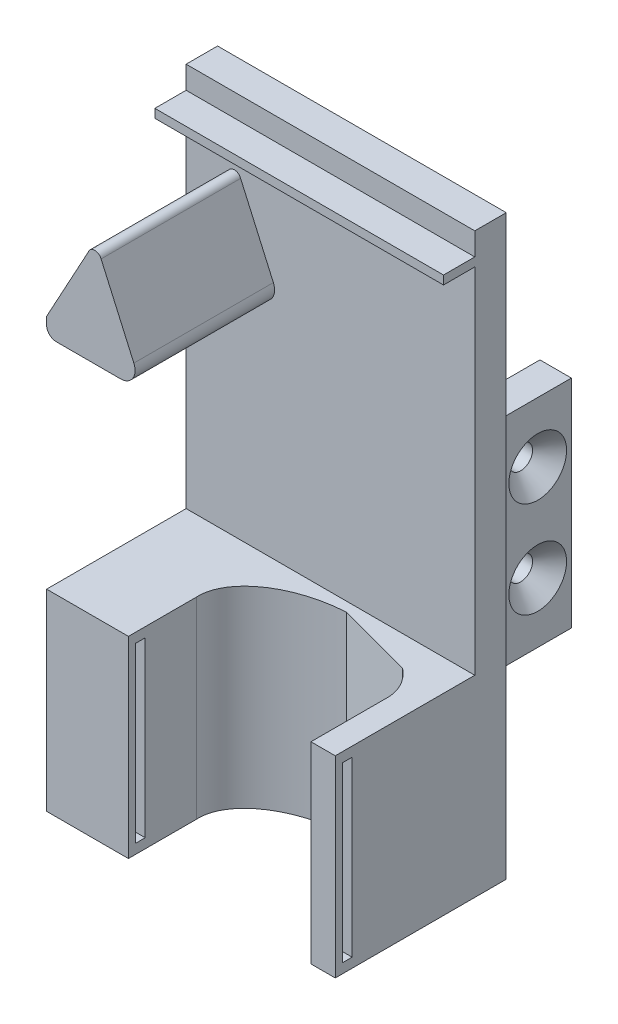
SolidWorks part; units mm, degrees
ref_plane "Front Plane" through (0, 0, 0) normal (0, 0, 1) x (1, 0, 0)
ref_plane "Top Plane" through (0, 0, 0) normal (0, 1, 0) x (1, 0, 0)
ref_plane "Right Plane" through (0, 0, 0) normal (1, 0, 0) x (0, 0, -1)
sketch "Sketch1" plane through (0, 0, 0) normal (0, 0, 1) x (1, 0, 0)
  line L1 (-30, 60) -> (30, 60)
  line L2 (-30, 60) -> (-30, -60)
  line L3 (-30, -60) -> (30, -60)
  line L4 (30, 60) -> (30, -60)
  line L5 (-30, 60) -> (30, -60) construction
  line L6 (-30, -60) -> (30, 60) construction
  point P0 (0, 0)
  dimension "D1" = 60
  dimension "D2" = 120
extrude "Boss-Extrude1" add sketch "Sketch1" along normal blind 6.54
sketch "Sketch7" plane through (0, 0, 6.54) normal (0, 0, 1) x (1, 0, 0)
  line L0 (-10, 25.5339) -> (-18.6733, 45.1016)
  line L1 (-30, 25.5339) -> (-10, 25.5339)
  line L6 (30, -60) -> (30, 60) construction
  line L15 (-21.3057, 45.0714) -> (-30, 29.1154)
  line L16 (-30, 60) -> (-30, -60) construction
  line L18 (-30, 29.1154) -> (-30, 25.5339)
  line L19 (30, 60) -> (-30, 60) construction
  arc A1 (-21.3057, 45.0714) -> (-18.6733, 45.1016) centre (-19.9839, 44.595) cw
  point P3 (-20, 46)
  dimension "D1" = 14
  dimension "D3" = 20
  dimension "D4" = 40
  dimension "D2" = 50
sketch "Sketch10" plane through (0, 0, 0) normal (0, 0, -1) x (-1, 0, 0)
  line L1 (20, 20) -> (26.54, 20)
  line L2 (-20, -25) -> (-20, 20)
  line L4 (-20, 20) -> (-26.54, 20)
  line L7 (20, -25) -> (20, 20)
  line L10 (-26.54, 20) -> (-26.54, -25)
  line L11 (-26.54, -25) -> (-20, -25)
  line L12 (26.54, 20) -> (26.54, -25)
  line L13 (26.54, -25) -> (20, -25)
  dimension "D1" = 6.54
  dimension "D2" = 20
  dimension "D3" = 6.54
  dimension "D4" = 20
  dimension "D5" = 45
  dimension "D6" = 45
extrude "Boss-Extrude5" add sketch "Sketch10" along normal blind 17
sketch "Sketch17" plane through (0, 0, 6.54) normal (0, 0, 1) x (1, 0, 0)
  line L0 (-30, 60) -> (-30, -60) construction
  line L1 (-30, -20) -> (30, -20)
  line L2 (-30, -20) -> (-30, -60)
  line L3 (-30, -60) -> (30, -60)
  line L4 (30, -20) -> (30, -60)
  line L5 (30, -60) -> (30, 60) construction
  line L6 (-30, -60) -> (30, -60) construction
  line L7 (30, 60) -> (-30, 60) construction
  dimension "D1" = 40
  dimension "D2" = 0
  dimension "D3" = 80
extrude "Boss-Extrude6" add sketch "Sketch17" along normal blind 29
sketch "Sketch18" plane through (0, -20, 0) normal (0, 1, 0) x (1, 0, 0)
  line L0 (5.335, -8.5264) -> (21.2913, -12.8258)
  line L1 (30, -35.54) -> (30, -6.54) construction
  line L2 (30, -35.54) -> (-30, -35.54) construction
  ellipse E0 centre (5.9723, -20.3092) end of major axis (24.9445, -19.283) minor radius 11.8 (5.335, -8.5264) -> (21.2913, -12.8258) ccw
  dimension "D1" = 43
  dimension "D2" = 5.0555
  dimension "D3" = 3.448
extrude "Cut-Extrude1" cut sketch "Sketch18" against normal up to next contours E0 L0
sketch "Sketch21" plane through (0, 0, 35.54) normal (0, 0, 1) x (1, 0, 0)
  line L0 (30, -20) -> (-30, -20) construction
  line L1 (-13, -20) -> (24.9445, -20)
  line L2 (-13, -20) -> (-13, -60)
  line L3 (-13, -60) -> (24.9445, -60)
  line L4 (24.9445, -20) -> (24.9445, -60)
  line L5 (-30, -60) -> (30, -60) construction
  line L6 (30, -60) -> (30, -20) construction
  dimension "D1" = 5.0555
  dimension "D2" = 43
extrude "Cut-Extrude2" cut sketch "Sketch21" against normal up to next contours L2 L3 L4 L1
sketch "Sketch23" plane through (-13, 0, 0) normal (1, 0, 0) x (0, 0, -1)
  line L0 (-35.54, -20) -> (-35.54, -60) construction
  line L1 (-34.04, -22) -> (-32.04, -22)
  line L2 (-34.04, -22) -> (-34.04, -58)
  line L3 (-34.04, -58) -> (-32.04, -58)
  line L4 (-32.04, -22) -> (-32.04, -58)
  line L5 (-21.3353, -60) -> (-35.54, -60) construction
  line L6 (-21.3353, -20) -> (-35.54, -20) construction
  dimension "D1" = 3.5
  dimension "D2" = 2
  dimension "D3" = 2
  dimension "D4" = 2
  dimension "D5" = 36
extrude "Cut-Extrude3" cut sketch "Sketch23" against normal blind 9
sketch "Sketch24" plane through (24.9445, 0, 0) normal (-1, 0, 0) x (0, 0, 1)
  line L0 (20.076, -60) -> (35.54, -60) construction
  line L1 (32.04, -22) -> (34.04, -22)
  line L2 (32.04, -22) -> (32.04, -58)
  line L3 (32.04, -58) -> (34.04, -58)
  line L4 (34.04, -22) -> (34.04, -58)
  line L5 (20.076, -20) -> (35.54, -20) construction
  line L6 (35.54, -20) -> (35.54, -60) construction
  dimension "D1" = 2
  dimension "D2" = 2
  dimension "D3" = 2
  dimension "D4" = 3.5
extrude "Cut-Extrude4" cut sketch "Sketch24" against normal blind 9
hole_wizard "CSK for M3 Flat Head Machine Screw4" positions "3DSketch2" profile "Sketch27" countersink size "M3" standard "ANSI Metric" end condition up to next
sketch3d "3DSketch2"
  line L4 (26.54, -25, -17) -> (26.54, -25, 0) construction
  line L6 (26.54, 20, -17) -> (26.54, 20, 0) construction
  line L7 (30, -60, 0) -> (30, 60, 0) construction
  line L8 (26.54, 20, 0) -> (26.54, -25, 0) construction
  point P14 (26.54, -12.5, -10)
  point P26 (26.54, 7.5, -10)
  point P33 (0, 0, 0)
  point P36 (0, 0, 0)
  dimension "D1" = 10
  dimension "D5" = 10.5817
  dimension "D2" = 12.5
  dimension "D3" = 12.5
  dimension "D4" = 10
sketch "Sketch27" plane through (26.54, -12.5, -10) normal (0, 1, 0) x (0, 0, -1)
  line L0 (0, 0) -> (0, 6.54)
  line L1 (0, 6.54) -> (2.465, 6.54)
  line L2 (2.465, 6.54) -> (2.465, 3.535)
  line L3 (2.465, 3.535) -> (6, 0)
  line L5 (6, 0) -> (0, 0)
  line L6 (-2.465, 3.535) -> (-6, 0) construction
  line L11 (0, -6.35) -> (0, 107.95) construction
  dimension "Thru Hole Dia." = 4.93
  dimension "Thru Hole Depth" = 6.54
  dimension "Near C'Sink Dia." = 12
  dimension "Near C'Sink Angle" = 90
hole_wizard "CSK for M3 Flat Head Machine Screw5" positions "3DSketch3" profile "Sketch29" countersink size "M3" standard "ANSI Metric" end condition up to next
sketch3d "3DSketch3"
  line L2 (-26.54, 20, -17) -> (-26.54, 20, 0) construction
  line L3 (-26.54, -25, -17) -> (-26.54, -25, 0) construction
  line L4 (-26.54, -25, 0) -> (-26.54, 20, 0) construction
  point P10 (-26.54, -12.5, -10)
  point P13 (-26.54, 7.5, -10)
  dimension "D1" = 10
  dimension "D3" = 12.5
  dimension "D2" = 10
  dimension "D4" = 12.5
sketch "Sketch29" plane through (-26.54, -12.5, -10) normal (0, 1, 0) x (0, 0, 1)
  line L0 (0, 0) -> (0, 6.54)
  line L1 (0, 6.54) -> (2.465, 6.54)
  line L2 (2.465, 6.54) -> (2.465, 3.535)
  line L3 (2.465, 3.535) -> (6, 0)
  line L5 (6, 0) -> (0, 0)
  line L6 (-2.465, 3.535) -> (-6, 0) construction
  line L11 (0, -6.35) -> (0, 107.95) construction
  dimension "Thru Hole Dia." = 4.93
  dimension "Thru Hole Depth" = 6.54
  dimension "Near C'Sink Dia." = 12
  dimension "Near C'Sink Angle" = 90
extrude "Boss-Extrude8" add sketch "Sketch7" along normal blind 29
sketch "Sketch36" plane through (0, 0, 6.54) normal (0, 0, 1) x (1, 0, 0)
  line L0 (-30, 53.5) -> (30, 53.5)
  line L1 (30, 60) -> (-30, 60) construction
  line L2 (-30, 60) -> (-30, 29.1154) construction
  line L3 (-30, 55.3) -> (30, 55.3)
  line L4 (30, -20) -> (30, 60) construction
  line L5 (-30, 55.3) -> (-30, 53.5)
  line L6 (30, 55.3) -> (30, 53.5)
  dimension "D1" = 6.5
  dimension "D2" = 4.7
extrude "Boss-Extrude9" add sketch "Sketch36" along normal blind 6.5
fillet "Fillet1" radius 3 1 edges at (-10, 25.5339, 21.04)
fillet "Fillet2" radius 2 1 edges at (-30, 25.5339, 21.04)
